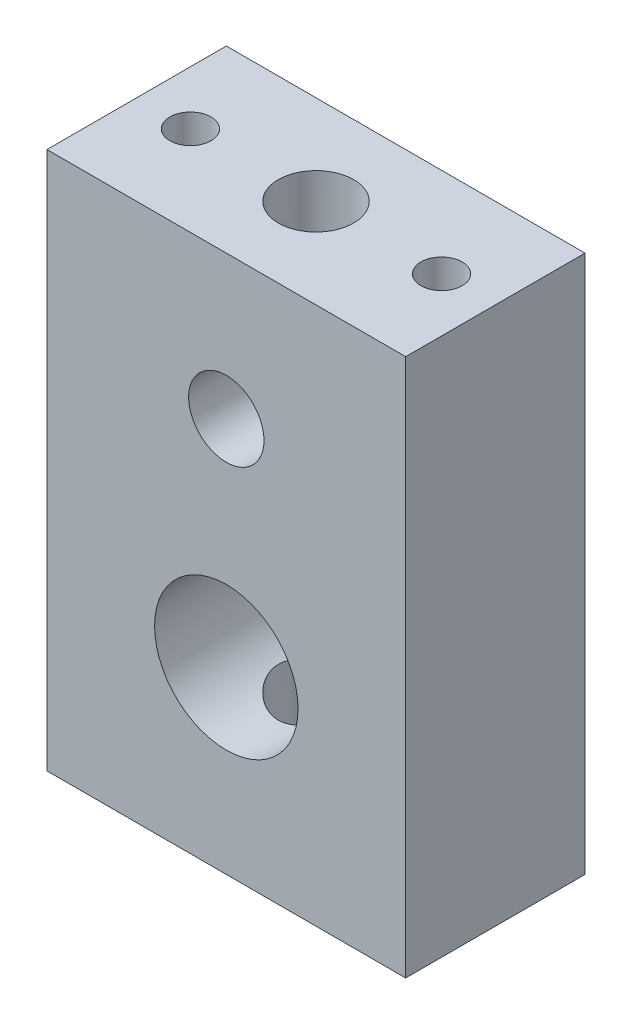
SolidWorks part; units mm, degrees
material "1060 Alloy"
ref_plane "Front Plane" through (0, 0, 0) normal (0, 0, 1) x (1, 0, 0)
ref_plane "Top Plane" through (0, 0, 0) normal (0, 1, 0) x (1, 0, 0)
ref_plane "Right Plane" through (0, 0, 0) normal (1, 0, 0) x (0, 0, -1)
sketch "Sketch1" plane through (0, 0, 0) normal (0, 0, 1) x (1, 0, 0)
  line L1 (0, 0) -> (20, 0)
  line L2 (0, 0) -> (0, 30)
  line L3 (0, 30) -> (20, 30)
  line L4 (20, 0) -> (20, 30)
  circle A0 centre (10, 10) radius 4
  circle A1 centre (10, 22) radius 2.1
  dimension "D3" = 8
  dimension "D6" = 8
  dimension "D7" = 4.2
  dimension "D1" = 30
  dimension "D2" = 20
  dimension "D4" = 10
  dimension "D5" = 10
extrude "Boss-Extrude1" add sketch "Sketch1" along normal blind 10
sketch "Sketch2" plane through (0, 30, 0) normal (0, 1, 0) x (1, 0, 0)
  line L0 (20, 0) -> (0, 0) construction
  line L1 (0, -10) -> (0, 0) construction
  line L2 (20, -10) -> (20, 0) construction
  circle A0 centre (3, -5) radius 1.15
  circle A1 centre (17, -5) radius 1.15
  circle A2 centre (10, -5) radius 2.1
  dimension "D1" = 2.3
  dimension "D5" = 4.2
  dimension "D2" = 5
  dimension "D3" = 3
  dimension "D4" = 3
  dimension "D6" = 10
extrude "Cut-Extrude1" cut sketch "Sketch2" against normal through all
